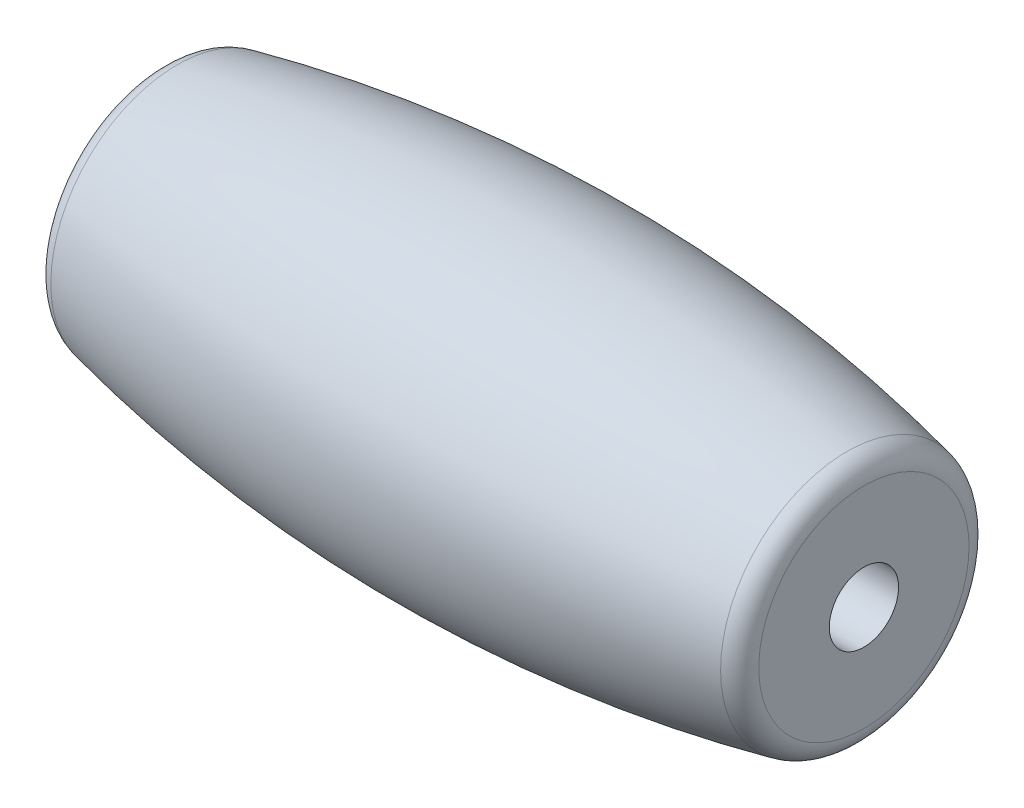
SolidWorks part; units mm, degrees
material "Rubber"
ref_plane "Front Plane" through (0, 0, 0) normal (0, 0, 1) x (1, 0, 0)
ref_plane "Top Plane" through (0, 0, 0) normal (0, 1, 0) x (1, 0, 0)
ref_plane "Right Plane" through (0, 0, 0) normal (1, 0, 0) x (0, 0, -1)
sketch "Sketch1" plane through (0, 0, 0) normal (0, 0, 1) x (1, 0, 0)
  line L0 (-32.1131, 0) -> (32.1131, 0) construction
  line L1 (-16.25, -5.6554) -> (16.25, -5.6554)
  line L2 (-16.25, -5.6554) -> (-16.25, 5.6554)
  line L3 (-16.25, 5.6554) -> (16.25, 5.6554)
  line L4 (16.25, -5.6554) -> (16.25, 5.6554)
  line L5 (-16.25, -5.6554) -> (16.25, 5.6554) construction
  line L6 (-16.25, 5.6554) -> (16.25, -5.6554) construction
  circle A0 centre (0, -65) radius 72.5
  circle A1 centre (0, 65) radius 72.5
  point P4 (-32.1131, 0)
  point P5 (32.1131, 0)
  point P6 (0, 7.5)
  point P10 (0, -7.5)
  point P11 (0, 0)
  point P16 (25.6493, 0)
  point P17 (23.3433, 0)
  point P18 (21.8658, 0)
  point P19 (0, 0)
  point P20 (18.7899, 0)
  point P21 (21.0871, 0)
  dimension "D1" = 145
  dimension "D2" = 15
  dimension "D3" = 32.5
revolve "Revolve1" add sketch "Sketch1" angle 360 about L0
sketch "Sketch2" plane through (0, 0, 0) normal (1, 0, 0) x (0, 0, -1)
  circle A0 centre (0, 0) radius 5.6554 construction
  circle A1 centre (0, 0) radius 5.6554
  circle A2 centre (0, 0) radius 1.6
  dimension "D1" = 3.2
extrude "Boss-Extrude1" add sketch "Sketch2" along normal through all and the other way through all
fillet "Fillet1" radius 1 2 edges at (-16.25, 0, 5.6554) (16.25, 0, -5.6554)
